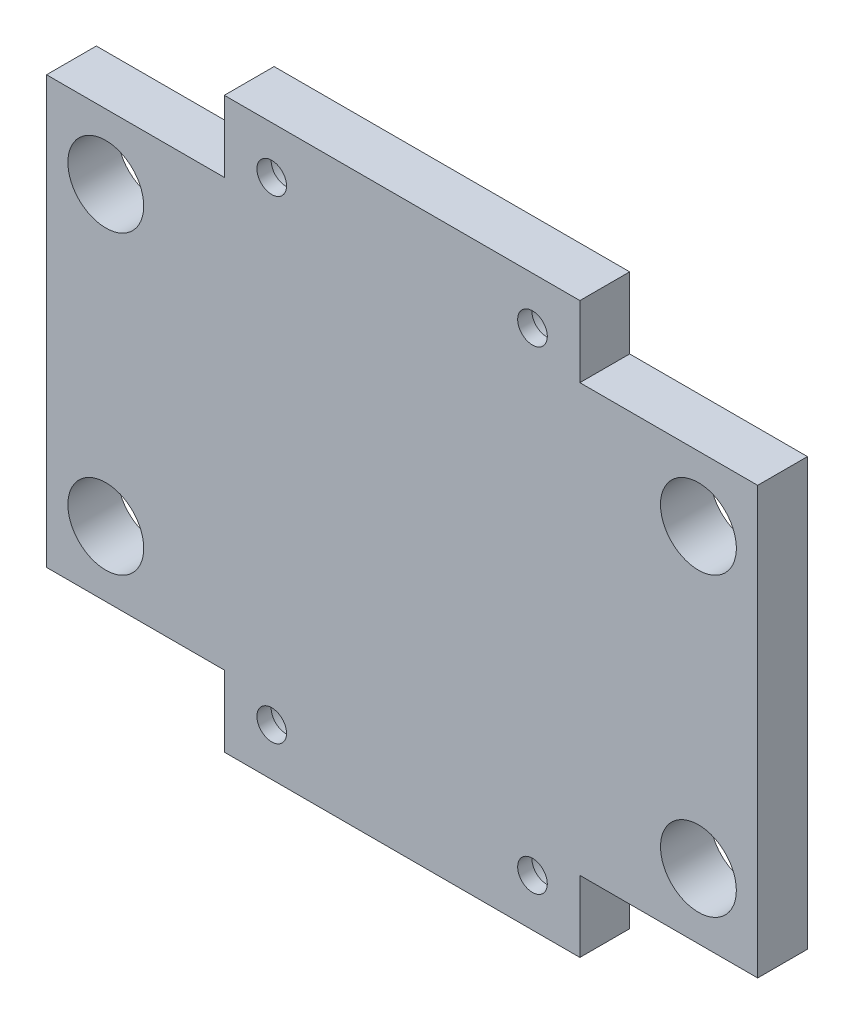
SolidWorks part; units mm, degrees
ref_plane "정면" through (0, 0, 0) normal (0, 0, 1) x (1, 0, 0)
ref_plane "윗면" through (0, 0, 0) normal (0, 1, 0) x (1, 0, 0)
ref_plane "우측면" through (0, 0, 0) normal (1, 0, 0) x (0, 0, -1)
sketch "스케치1" plane through (0, 0, 0) normal (0, 0, 1) x (1, 0, 0)
  line L0 (0, 0) -> (0, 24) construction
  line L1 (15, 24) -> (-15, 24)
  line L2 (-15, 24) -> (-15, 18)
  line L3 (-15, 18) -> (-30, 18)
  line L4 (-30, 18) -> (-30, -18)
  line L5 (0, 0) -> (-30, 0) construction
  line L6 (-15, -18) -> (-30, -18)
  line L7 (-15, -24) -> (-15, -18)
  line L8 (15, -24) -> (-15, -24)
  line L9 (15, -24) -> (15, -18)
  line L10 (15, -18) -> (30, -18)
  line L11 (30, 18) -> (30, -18)
  line L12 (15, 18) -> (30, 18)
  line L13 (15, 24) -> (15, 18)
  circle A0 centre (-25, 12.5) radius 3.2
  circle A1 centre (-11, 20) radius 1.25
  circle A2 centre (-11, -20) radius 1.25
  circle A3 centre (-25, -12.5) radius 3.2
  circle A4 centre (25, -12.5) radius 3.2
  circle A5 centre (11, -20) radius 1.25
  circle A6 centre (11, 20) radius 1.25
  circle A7 centre (25, 12.5) radius 3.2
  point P12 (0, 23.7745)
  point P29 (0, -24)
  dimension "D1" = 2.5
  dimension "D10" = 6.4
  dimension "D2" = 11
  dimension "D3" = 15
  dimension "D4" = 24
  dimension "D5" = 20
  dimension "D6" = 30
  dimension "D7" = 18
  dimension "D8" = 25
  dimension "D9" = 12.5
extrude "보스-돌출1" add sketch "스케치1" along normal blind 4.2
sketch "스케치2" plane through (0, 0, 0) normal (0, 0, -1) x (-1, 0, 0)
  circle A0 centre (-11, 20) radius 2.5
  circle A1 centre (11, 20) radius 2.5
  circle A2 centre (11, -20) radius 2.5
  circle A3 centre (-11, -20) radius 2.5
  dimension "D1" = 5
extrude "컷-돌출1" cut sketch "스케치2" against normal blind 3
